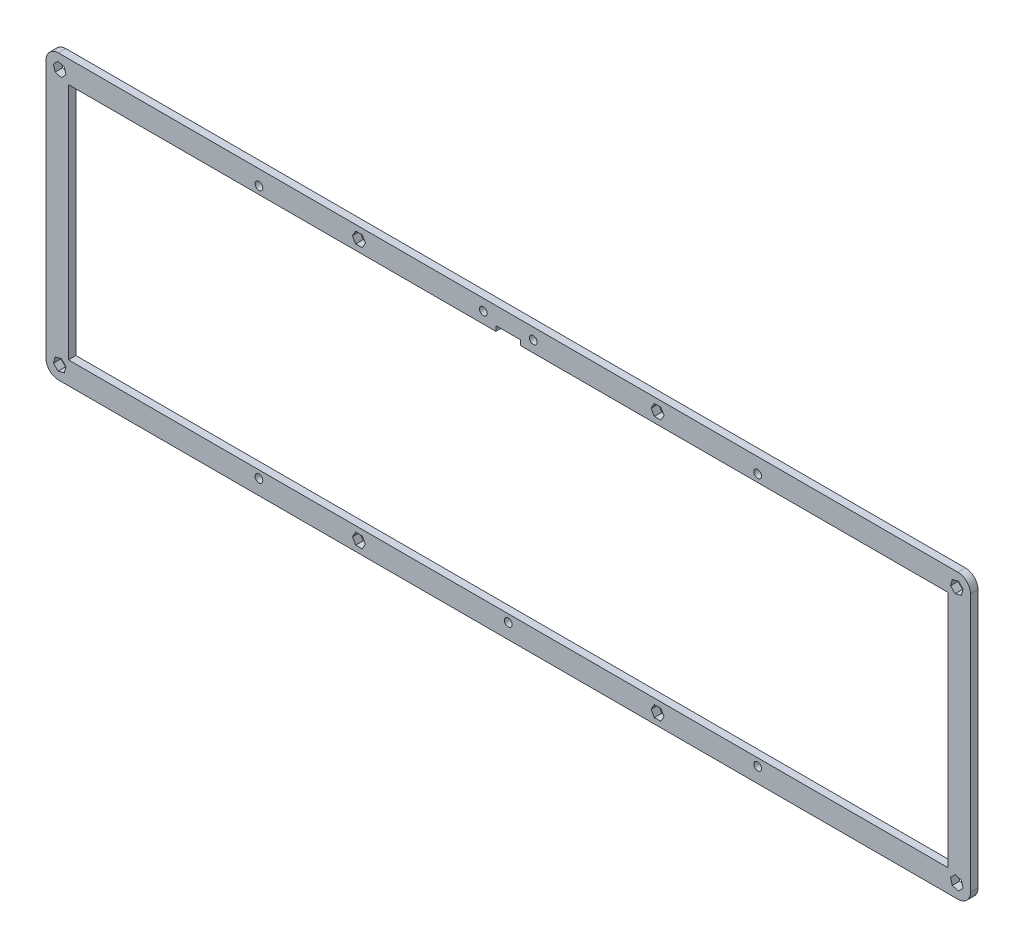
SolidWorks part; units mm, degrees
ref_plane "Front Plane" through (0, 0, 0) normal (0, 0, 1) x (1, 0, 0)
ref_plane "Top Plane" through (0, 0, 0) normal (0, 1, 0) x (1, 0, 0)
ref_plane "Right Plane" through (0, 0, 0) normal (1, 0, 0) x (0, 0, -1)
sketch "Model" plane through (0, 0, 0) normal (0, 0, 1) x (1, 0, 0)
  line L0 (0, 108.6) -> (0, 5)
  line L1 (365.775, 0) -> (5, 0)
  line L2 (370.775, 108.6) -> (370.775, 5)
  line L3 (5, 113.6) -> (365.775, 113.6)
  line L4 (9, 9) -> (361.775, 9)
  line L5 (361.775, 9) -> (361.775, 104.6)
  line L7 (365.9474, 110.6095) -> (367.7845, 108.7724)
  line L8 (367.7845, 108.7724) -> (367.1121, 106.2629)
  line L9 (367.1121, 106.2629) -> (364.6026, 105.5905)
  line L10 (364.6026, 105.5905) -> (362.7655, 107.4276)
  line L11 (362.7655, 107.4276) -> (363.4379, 109.9371)
  line L12 (363.4379, 109.9371) -> (365.9474, 110.6095)
  line L13 (4.8276, 110.6095) -> (2.9905, 108.7724)
  line L14 (2.9905, 108.7724) -> (3.6629, 106.2629)
  line L15 (3.6629, 106.2629) -> (6.1724, 105.5905)
  line L16 (6.1724, 105.5905) -> (8.0095, 107.4276)
  line L17 (8.0095, 107.4276) -> (7.3371, 109.9371)
  line L18 (7.3371, 109.9371) -> (4.8276, 110.6095)
  line L19 (365.9474, 2.9905) -> (367.7845, 4.8276)
  line L20 (367.7845, 4.8276) -> (367.1121, 7.3371)
  line L21 (367.1121, 7.3371) -> (364.6026, 8.0095)
  line L22 (364.6026, 8.0095) -> (362.7655, 6.1724)
  line L23 (362.7655, 6.1724) -> (363.4379, 3.6629)
  line L24 (363.4379, 3.6629) -> (365.9474, 2.9905)
  line L25 (126.799, 2.25) -> (124.201, 2.25)
  line L26 (124.201, 2.25) -> (122.9019, 4.5)
  line L27 (122.9019, 4.5) -> (124.201, 6.75)
  line L28 (124.201, 6.75) -> (126.799, 6.75)
  line L29 (126.799, 6.75) -> (128.0981, 4.5)
  line L30 (128.0981, 4.5) -> (126.799, 2.25)
  line L31 (4.8276, 2.9905) -> (2.9905, 4.8276)
  line L32 (2.9905, 4.8276) -> (3.6629, 7.3371)
  line L33 (3.6629, 7.3371) -> (6.1724, 8.0095)
  line L34 (6.1724, 8.0095) -> (8.0095, 6.1724)
  line L35 (8.0095, 6.1724) -> (7.3371, 3.6629)
  line L36 (7.3371, 3.6629) -> (4.8276, 2.9905)
  line L37 (9, 9) -> (9, 104.6)
  line L38 (126.799, 111.35) -> (124.201, 111.35)
  line L39 (124.201, 111.35) -> (122.9019, 109.1)
  line L40 (122.9019, 109.1) -> (124.201, 106.85)
  line L41 (124.201, 106.85) -> (126.799, 106.85)
  line L42 (126.799, 106.85) -> (128.0981, 109.1)
  line L43 (128.0981, 109.1) -> (126.799, 111.35)
  line L44 (243.976, 2.25) -> (246.574, 2.25)
  line L45 (246.574, 2.25) -> (247.8731, 4.5)
  line L46 (247.8731, 4.5) -> (246.574, 6.75)
  line L47 (246.574, 6.75) -> (243.976, 6.75)
  line L48 (243.976, 6.75) -> (242.6769, 4.5)
  line L49 (242.6769, 4.5) -> (243.976, 2.25)
  line L50 (243.976, 111.35) -> (246.574, 111.35)
  line L51 (246.574, 111.35) -> (247.8731, 109.1)
  line L52 (247.8731, 109.1) -> (246.574, 106.85)
  line L53 (246.574, 106.85) -> (243.976, 106.85)
  line L54 (243.976, 106.85) -> (242.6769, 109.1)
  line L55 (242.6769, 109.1) -> (243.976, 111.35)
  line L56 (185.3875, 113.6) -> (185.3875, 106.6) construction
  line L58 (180.3875, 106.6) -> (190.3875, 106.6)
  line L60 (180.3875, 106.6) -> (180.3875, 104.6)
  line L61 (190.3875, 106.6) -> (190.3875, 104.6)
  line L62 (180.3875, 104.6) -> (9, 104.6)
  line L63 (190.3875, 104.6) -> (361.775, 104.6)
  arc A0 (365.775, 0) -> (370.775, 5) centre (365.775, 5) ccw
  arc A1 (370.775, 108.6) -> (365.775, 113.6) centre (365.775, 108.6) ccw
  arc A2 (0, 5) -> (5, 0) centre (5, 5) ccw
  arc A3 (5, 113.6) -> (0, 108.6) centre (5, 108.6) ccw
  circle A4 centre (195.3875, 109.1) radius 1.55
  circle A5 centre (175.3875, 109.1) radius 1.55
  circle A6 centre (85.3875, 107.6) radius 1.55
  circle A7 centre (285.3875, 107.6) radius 1.55
  circle A8 centre (85.3875, 6) radius 1.55
  circle A9 centre (185.3875, 6) radius 1.55
  circle A10 centre (285.3875, 6) radius 1.55
  point P83 (185.3875, 106.6)
  dimension "D2" = 3.1
  dimension "D3" = 3.1
  dimension "D4" = 3.1
  dimension "D5" = 3.1
  dimension "D6" = 3.1
  dimension "D1" = 113.6
  dimension "D7" = 7
  dimension "D8" = 10
  dimension "D9" = 2
  dimension "D10" = 2
extrude "Boss-Extrude1" add sketch "Model" along normal blind 3
